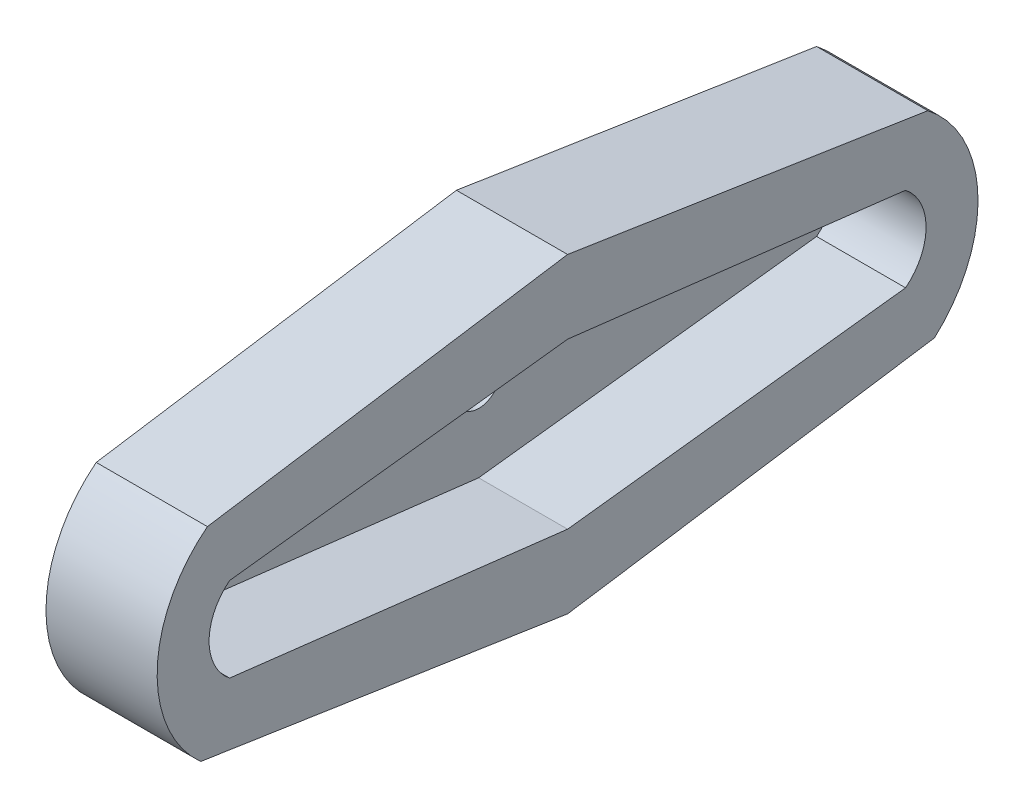
SolidWorks part; units mm, degrees
ref_plane "Front Plane" through (0, 0, 0) normal (0, 0, 1) x (1, 0, 0)
ref_plane "Top Plane" through (0, 0, 0) normal (0, 1, 0) x (1, 0, 0)
ref_plane "Right Plane" through (0, 0, 0) normal (1, 0, 0) x (0, 0, -1)
sketch "Sketch1" plane through (0, 0, 0) normal (1, 0, 0) x (0, 0, -1)
  line L0 (0, 7) -> (-16.2, 4.5)
  line L1 (-16.5, -4.5) -> (0, -7)
  line L4 (0, 3.7) -> (-15.2, 1.9)
  line L5 (-15.2, -1.9) -> (0, -3.7)
  line L10 (0, 0) -> (0, 22.8337) construction
  line L11 (15.2, -1.9) -> (0, -3.7)
  line L12 (0, 3.7) -> (15.2, 1.9)
  line L13 (16.5, -4.5) -> (0, -7)
  line L14 (0, 7) -> (16.2, 4.5)
  arc A0 (-16.2, 4.5) -> (-16.5, -4.5) centre (-12.5962, -0.1251) ccw
  arc A1 (-15.2, 1.9) -> (-15.2, -1.9) centre (-13.7067, 0) ccw
  arc A2 (15.2, 1.9) -> (15.2, -1.9) centre (13.7067, 0) cw
  arc A3 (16.2, 4.5) -> (16.5, -4.5) centre (12.5962, -0.1251) cw
  dimension "D1" = 2.5
  dimension "D2" = 2.5
  dimension "D3" = 1.8
  dimension "D4" = 1.8
  dimension "D5" = 15.2
  dimension "D6" = 0
  dimension "D7" = 16.2
  dimension "D8" = 0
  dimension "D9" = 0
  dimension "D11" = 15.2
  dimension "D12" = 16.5
  dimension "D13" = 0
extrude "Boss-Extrude1" add sketch "Sketch1" along normal blind 4
sketch "Sketch2" plane through (0, 0, 0) normal (1, 0, 0) x (0, 0, -1)
  line L0 (0, 7) -> (-16.2, 4.5)
  line L1 (-16.5, -4.5) -> (0, -7)
  line L2 (0, -8.5344) -> (0, 10.0066) construction
  line L3 (16.5, -4.5) -> (0, -7)
  line L4 (0, 7) -> (16.2, 4.5)
  arc A0 (-16.2, 4.5) -> (-16.5, -4.5) centre (-12.5962, -0.1251) ccw
  arc A1 (16.2, 4.5) -> (16.5, -4.5) centre (12.5962, -0.1251) cw
  circle A2 centre (0, 0) radius 1
  dimension "D1" = 2
extrude "Boss-Extrude2" add sketch "Sketch2" against normal blind 1
